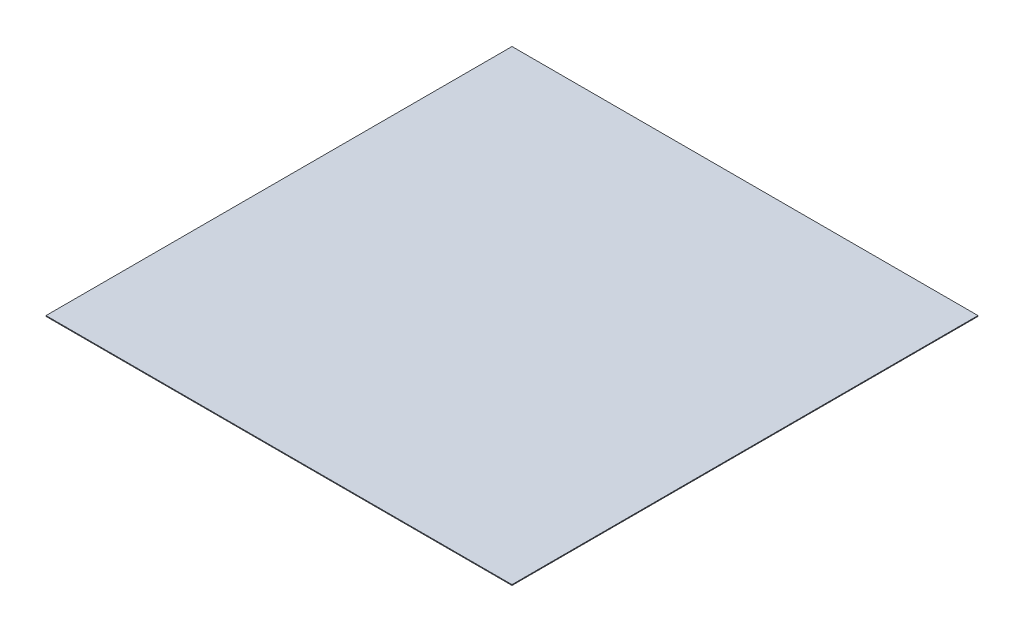
SolidWorks part; units mm, degrees
ref_plane "Front" through (0, 0, 0) normal (0, 0, 1) x (1, 0, 0)
ref_plane "Top" through (0, 0, 0) normal (0, 1, 0) x (1, 0, 0)
ref_plane "Right" through (0, 0, 0) normal (1, 0, 0) x (0, 0, -1)
sketch "Sketch1" plane through (0, 0, 0) normal (0, 1, 0) x (1, 0, 0)
  line L1 (-381, 381) -> (381, 381)
  line L2 (-381, 381) -> (-381, -381)
  line L3 (-381, -381) -> (381, -381)
  line L4 (381, 381) -> (381, -381)
  line L5 (-381, 381) -> (381, -381) construction
  line L6 (-381, -381) -> (381, 381) construction
  point P0 (0, 0)
  dimension "D1" = 762
  dimension "D2" = 762
extrude "Boss-Extrude1" add sketch "Sketch1" along normal blind 1.27
